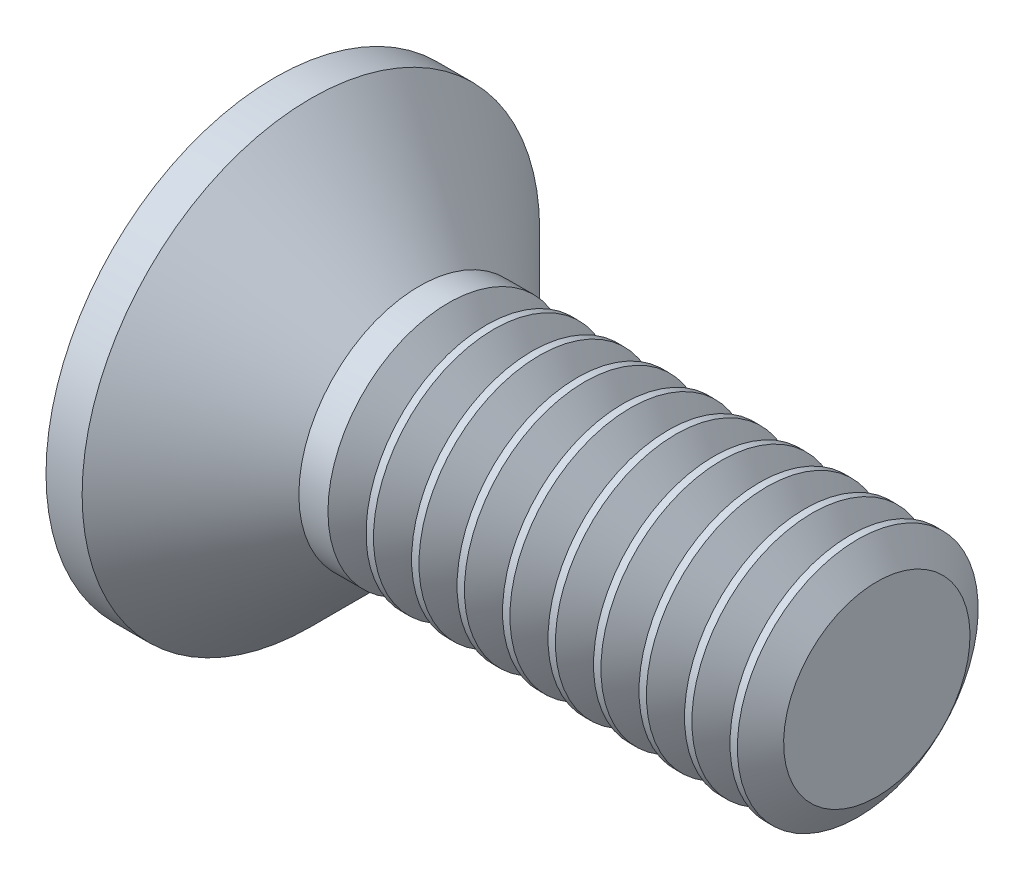
SolidWorks part; units mm, degrees
ref_plane "Plane1" through (0, 0, 0) normal (0, 0, 1) x (1, 0, 0)
ref_plane "Plane2" through (0, 0, 0) normal (0, 1, 0) x (1, 0, 0)
ref_plane "Plane3" through (0, 0, 0) normal (1, 0, 0) x (0, 0, -1)
sketch "BodySke" plane through (0, 0, 0) normal (0, 0, 1) x (1, 0, 0)
  line L0 (0, 0) -> (0, 1.9)
  line L1 (0, 1.9) -> (0.3, 1.9)
  line L2 (1.2, 1) -> (5, 1)
  line L3 (5, 1) -> (5, 0)
  line L4 (5, 0) -> (0, 0)
  line L5 (-6.35, 0) -> (82.55, 0) construction
  line L6 (1.2, -1) -> (5, -1) construction
  line L7 (0.3, -1.9) -> (1.2, -1) construction
  line L8 (0.3, 1.9) -> (1.2, 1)
  line L9 (0, -1.9) -> (0.3, -1.9) construction
  line L10 (1.6, 2.5875) -> (1.6, -6.9375) construction
  line L11 (0, 6.35) -> (0, -3.175) construction
  dimension "Diameter" = 2
  dimension "Length" = 5
  dimension "Head_ht" = 1.2
  dimension "Head_dia" = 3.8
  dimension "Head_ang" = 90
  dimension "D6" = 0.3
  dimension "Advance" = 0.4
  dimension "Thread_nom" = 5
revolve "Base-Revolve" add sketch "BodySke" angle 360 about L5
cosmetic thread "ThreadCosmetic" [suppressed] parameters "Thread_length"=3.4, "Thread_minor"=1.548
sketch "Sketch2" plane through (0, 0, 0) normal (-1, 0, 0) x (0, 0, 1)
  line L0 (-1.9, -0.35) -> (1.9, -0.35)
  line L1 (-1.9, -0.35) -> (-1.9, 0.35)
  line L2 (1.9, 0.35) -> (-1.9, 0.35)
  line L3 (1.9, 0.35) -> (1.9, -0.35)
  dimension "D1" = 0.35
  dimension "Slot_width" = 0.7
  dimension "D2" = 3.8
  dimension "D3" = 1.9
extrude "Slot" [suppressed] cut sketch "Sketch2" against normal blind 0.6
sketch "Sketch3" plane through (0, 0, 0) normal (-1, 0, 0) x (0, 0, 1)
  line L0 (-0.265, 1.07) -> (0.265, 1.07)
  line L1 (0.265, 1.07) -> (0.265, -1.07)
  line L2 (0.265, -1.07) -> (-0.265, -1.07)
  line L3 (-0.265, -1.07) -> (-0.265, 1.07)
  dimension "D1" = 1.07
  dimension "Cross_dia" = 2.14
  dimension "D2" = 0.265
  dimension "Cross_width" = 0.53
ref_plane "Plane4" through (1.54, 0, 0) normal (-1, 0, 0) x (0, 0, 1)
sketch "Sketch4" plane through (1.54, 0, 0) normal (-1, 0, 0) x (0, 0, 1)
  line L0 (-0.1325, 0.1325) -> (0.1325, 0.1325)
  line L3 (0.1325, 0.1325) -> (0.1325, -0.1325)
  line L4 (0.1325, -0.1325) -> (-0.1325, -0.1325)
  line L5 (-0.1325, -0.1325) -> (-0.1325, 0.1325)
  dimension "D1" = 0.265
  dimension "D2" = 0.265
  dimension "D3" = 0.1325
  dimension "D4" = 0.1325
loft "Cross" cut profiles "Sketch3", "Sketch4"
pattern_circular "CirPattern1" count 2 every 90 about axis through (0, 0, 0) along (1, 0, 0) of "Cross"
sketch "ThdSchSke" plane through (0, 0, 0) normal (0, 0, 1) x (1, 0, 0)
  line L0 (1.6, -0.774) -> (1.4418, -1)
  line L1 (1.6, -0.774) -> (1.7582, -1)
  line L2 (1.7582, -1) -> (1.7582, -1.25)
  line L3 (-3.175, 0) -> (5.1513, 0) construction
  line L5 (1.7582, -1.25) -> (1.4418, -1.25)
  line L6 (1.4418, -1.25) -> (1.4418, -1)
  line L7 (0, 1.9) -> (0, -1.9) construction
  dimension "Thread_minor" = 1.548
  dimension "Diameter" = 2
  dimension "Start" = 1.6
  dimension "SideAngle" = 55
  dimension "VeeAngle" = 70
  dimension "Overcut" = 2.5
revolve "ThreadSchematic" cut sketch "ThdSchSke" angle 360 about L3
pattern_linear "ThdSchPat" count 10 spacing 0.3778 along (1, 0, 0) of "ThreadSchematic"
equation "\"D1@Sketch3\" = \"Cross_dia@Sketch3\" / 2"
equation "\"D2@Sketch3\" = \"Cross_width@Sketch3\" / 2"
equation "\"D1@Sketch4\" = \"Cross_width@Sketch3\" *.5"
equation "\"D2@Sketch4\" = \"D1@Sketch4\""
equation "\"D4@Sketch4\" = \"D2@Sketch4\" / 2"
equation "\"D3@Sketch4\" = \"D1@Sketch4\" / 2"
equation "\"D1@Sketch2\" = \"Slot_width@Sketch2\" / 2"
equation "\"D2@Sketch2\" = \"Head_dia@BodySke\""
equation "\"D3@Sketch2\" = \"D2@Sketch2\" / 2"
equation "\"Thread_length@ThreadCosmetic\" = ((sgn( (\"Length@BodySke\" - \"Advance@BodySke\" - \"Head_ht@BodySke\" ) - \"Thread_nom@BodySke\" )-1)*( (\"Length@BodySke\" - \"Advance@BodySke\" - \"Head_ht@BodySke\" ) - \"Thread_nom@BodySke\" ))/-2+ \"Thread_nom@BodySke\""
equation "\"Thread_minor@ThdSchSke\" = \"Thread_minor@ThreadCosmetic\""
equation "\"Diameter@ThdSchSke\" = \"Diameter@BodySke\""
equation "\"Overcut@ThdSchSke\" = \"Diameter@BodySke\" * 1.25"
equation "\"Start@ThdSchSke\" = 0.000001 + \"Length@BodySke\" - \"Thread_length@ThreadCosmetic\"  '---Countersunk---"
equation "\"Num_threads@ThdSchPat\" = int( \"Thread_length@ThreadCosmetic\" / \"Advance@BodySke\" + 0.999 )  + 1"
equation "\"Advance@ThdSchPat\" = \"Thread_length@ThreadCosmetic\" /  (\"Num_threads@ThdSchPat\" - 1) 'relax it"
